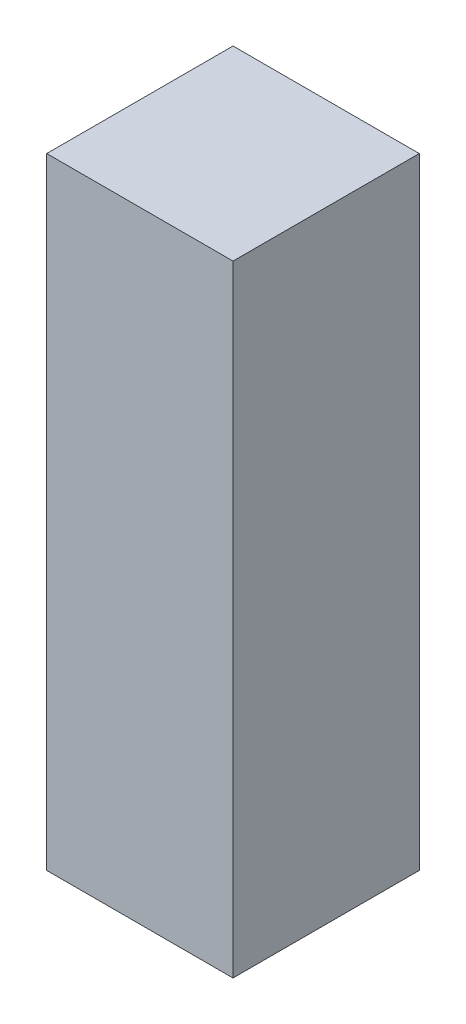
SolidWorks part; units mm, degrees
ref_plane "Front Plane" through (0, 0, 0) normal (0, 0, 1) x (1, 0, 0)
ref_plane "Top Plane" through (0, 0, 0) normal (0, 1, 0) x (1, 0, 0)
ref_plane "Right Plane" through (0, 0, 0) normal (1, 0, 0) x (0, 0, -1)
sketch "Sketch1" plane through (0, 0, 0) normal (0, 1, 0) x (1, 0, 0)
  line L1 (0, 0) -> (3, 0)
  line L2 (0, 0) -> (0, 3)
  line L3 (0, 3) -> (3, 3)
  line L4 (3, 0) -> (3, 3)
  dimension "D1" = 3
  dimension "D2" = 3
extrude "Boss-Extrude1" add sketch "Sketch1" along normal blind 10
